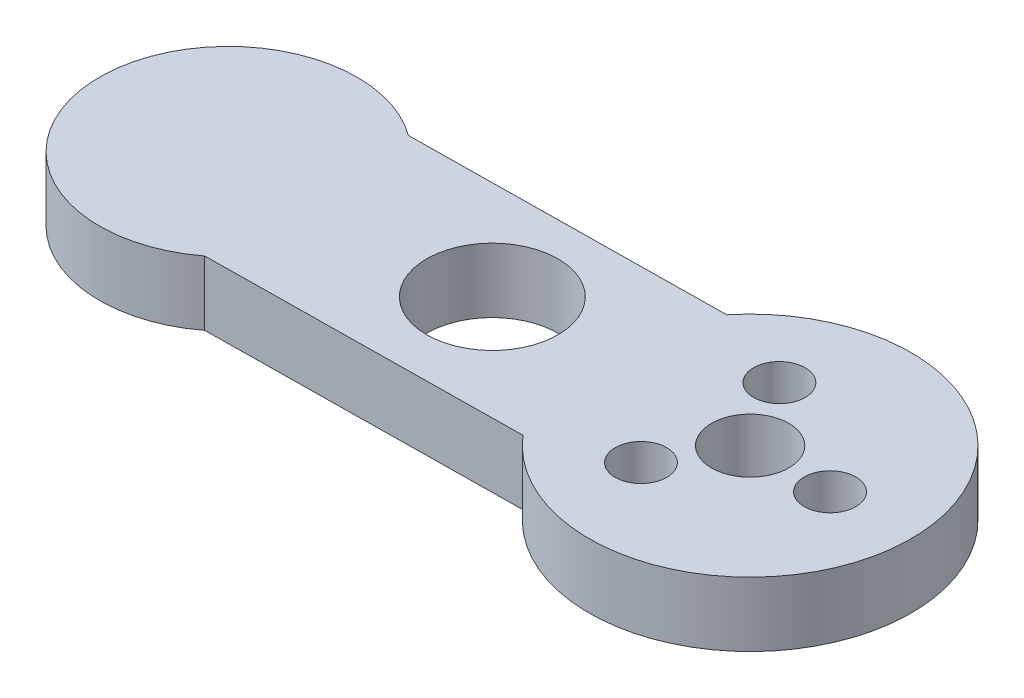
SolidWorks part; units mm, degrees
ref_plane "Front Plane" through (0, 0, 0) normal (0, 0, 1) x (1, 0, 0)
ref_plane "Top Plane" through (0, 0, 0) normal (0, 1, 0) x (1, 0, 0)
ref_plane "Right Plane" through (0, 0, 0) normal (1, 0, 0) x (0, 0, -1)
sketch "Sketch1" plane through (0, 0, 0) normal (0, 1, 0) x (1, 0, 0)
  line L0 (-55, 0) -> (55, 0) construction
  line L1 (0, 0) -> (-39.997, -0.4887) construction
  line L2 (0, 0) -> (0, 33) construction
  line L3 (0, -55) -> (0, 55) construction
  line L5 (-9.5062, -8.1167) -> (-33.8997, -8.4148)
  line L6 (2, 12.339) -> (-2, 12.339)
  line L10 (-9.7017, 7.8821) -> (-34.0952, 7.584)
  circle A0 centre (0, 0) radius 12.5
  circle A1 centre (0, 0) radius 3
  circle A2 centre (6.2, 0) radius 2
  circle A5 centre (-39.997, -0.4887) radius 10
  circle A6 centre (-3.1, -5.3694) radius 2
  circle A7 centre (-3.1, 5.3694) radius 2
  circle A8 centre (0, 0) radius 9.5 construction
  circle A9 centre (-20, 0) radius 5.1
  point P14 (0, 0)
  point P36 (0, 0)
  dimension "D1" = 25
  dimension "D2" = 6
  dimension "D3" = 4
  dimension "D7" = 20
  dimension "D8" = 19
  dimension "D9" = 10.2
  dimension "D4" = 6.2
  dimension "D5" = 0.7
  dimension "D6" = 40
  dimension "D10" = 8
  dimension "D11" = 20
  dimension "D13" = 3
extrude "Boss-Extrude1" add sketch "Sketch1" along normal blind 5
